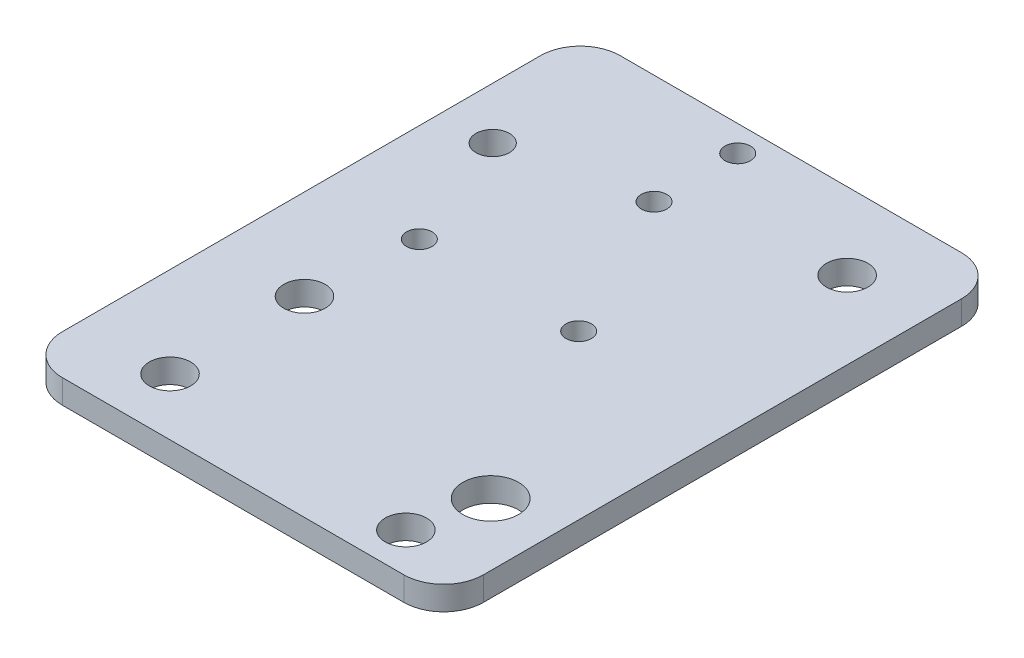
SolidWorks part; units mm, degrees
material "6061 合金"
ref_plane "前视基准面" through (0, 0, 0) normal (0, 0, 1) x (1, 0, 0)
ref_plane "上视基准面" through (0, 0, 0) normal (0, 1, 0) x (1, 0, 0)
ref_plane "右视基准面" through (0, 0, 0) normal (1, 0, 0) x (0, 0, -1)
sketch "草图1" plane through (0, 0, 0) normal (0, 1, 0) x (1, 0, 0)
  line L0 (-7.5, -1000) -> (-7.5, 49000) construction
  line L1 (-17.5, -35) -> (17.5, -35)
  line L2 (-17.5, -35) -> (-17.5, 35)
  line L3 (-17.5, 35) -> (17.5, 35)
  line L4 (17.5, -35) -> (17.5, 35)
  line L5 (0, 35) -> (0, -35) construction
  line L6 (-17.5, 0) -> (17.5, 0) construction
  circle A0 centre (-7.5, 22.5) radius 2.6
  circle A1 centre (-7.5, 0) radius 2.6
  circle A2 centre (-7.5, -22.5) radius 2.6
  circle A3 centre (-7.5, 10) radius 2.6
  circle A4 centre (-7.5, -10) radius 2.6
  point P0 (0, 0)
  dimension "D1" = 45
  dimension "D2" = 5.2
  dimension "D4" = 22.5
  dimension "D8" = 20
  dimension "D5" = 10
  dimension "D6" = 70
  dimension "D7" = 35
  dimension "D3" = 3
extrude "主板" add sketch "草图1" along normal blind 3
sketch "草图2" plane through (0, 3, 0) normal (0, 1, 0) x (1, 0, 0)
  line L0 (-1000, 0) -> (49000, 0) construction
  circle A0 centre (10, 0) radius 2.1
  dimension "D1" = 4.2
  dimension "D2" = 10
extrude "M4铝柱" cut sketch "草图2" against normal blind 3
sketch "草图3" plane through (0, 3, 0) normal (0, 1, 0) x (1, 0, 0)
  circle A0 centre (-7.5, 0) radius 2.6 construction
  circle A1 centre (-7.5, 0) radius 2.6 construction
  circle A2 centre (-7.5, -10) radius 2.6 construction
  circle A3 centre (-7.5, 10) radius 2.6 construction
  circle A4 centre (-7.5, -10) radius 2.6
  circle A5 centre (-7.5, 10) radius 2.6
extrude "填补" add sketch "草图3" against normal through all
sketch "草图4" plane through (0, 3, 0) normal (0, 1, 0) x (1, 0, 0)
  line L1 (-7.5, -22.5) -> (10, -22.5) construction
  line L2 (-7.5, -22.5) -> (-7.5, 22.5) construction
  line L3 (-7.5, 22.5) -> (10, 22.5) construction
  line L4 (10, -22.5) -> (10, 22.5) construction
  line L5 (1.25, 22.5) -> (1.25, -22.5) construction
  line L6 (-7.5, 0) -> (10, 0) construction
  circle A0 centre (-7.5, 22.5) radius 2.6 construction
  circle A1 centre (10, 0) radius 2.1 construction
  circle A2 centre (10, 22.5) radius 2.1
  circle A3 centre (10, -22.5) radius 2.1
  point P0 (1.25, 0)
extrude "摩擦轮垫板" cut sketch "草图4" against normal through all
sketch "草图5" plane through (0, 3, 0) normal (0, 1, 0) x (1, 0, 0)
  line L0 (17.5, 35) -> (-17.5, 35) construction
  line L1 (17.5, -35) -> (66.5, -35) construction
  line L2 (17.5, -35) -> (17.5, 35) construction
  line L3 (17.5, 35) -> (66.5, 35) construction
  line L4 (66.5, -35) -> (66.5, 35) construction
  line L5 (0, -1000) -> (0, 49000) construction
  line L6 (-17.5, 35) -> (-66.5, 35)
  line L7 (-66.5, -35) -> (-66.5, 35)
  line L8 (-17.5, -35) -> (-66.5, -35)
  line L9 (-17.5, -35) -> (-17.5, 35)
  dimension "D1" = 49
extrude "EXTRA" add sketch "草图5" against normal through all
fillet "圆角5" [suppressed] radius 5
sketch "草图6" plane through (0, 3, 0) normal (0, 1, 0) x (1, 0, 0)
  line L0 (-999.7092, 0) -> (49000.2908, 0) construction
  line L2 (-40.5, -989.9006) -> (-40.5, 49010.0994) construction
  line L3 (-7.5, -977.5) -> (-7.5, 49022.5) construction
  circle A0 centre (-44.5, 0) radius 2.1
  circle A1 centre (-36.5, 0) radius 2.1
  dimension "D1" = 4.2
  dimension "D3" = 8
  dimension "D2" = 33
extrude "垂直板接件" cut sketch "草图6" against normal blind 10
sketch "草图7" plane through (0, 3, 0) normal (0, 1, 0) x (1, 0, 0)
  line L0 (-1000, 0) -> (49000, 0) construction
  line L1 (0, -1000) -> (0, 49000) construction
  circle A0 centre (-60, 17.5) radius 2.1
  circle A1 centre (-60, 17.5) radius 5 construction
  circle A2 centre (-60, -17.5) radius 2.1
  dimension "D1" = 4.2
  dimension "D2" = 10
  dimension "D4" = 60
  dimension "D3" = 35
extrude "ETRA铝柱" cut sketch "草图7" against normal blind 10
sketch "草图8" [suppressed] plane through (0, 3, 0) normal (0, 1, 0) x (1, 0, 0)
  line L0 (-17.5, 30) -> (-17.5, -30) construction
  line L1 (17.5, 30) -> (-17.5, 30)
  line L2 (17.5, 30) -> (17.5, 55)
  line L3 (17.5, 55) -> (-17.5, 55)
  line L4 (-17.5, 30) -> (-17.5, 55)
  line L5 (0, -1000) -> (0, 49000) construction
  line L6 (-1000, 0) -> (49000, 0) construction
  line L7 (17.5, -55) -> (-17.5, -55)
  line L8 (-17.5, -30) -> (-17.5, -55)
  line L9 (17.5, -30) -> (-17.5, -30)
  line L10 (17.5, -30) -> (17.5, -55)
  dimension "D1" = 110
extrude "ETRA2" [suppressed] add sketch "草图8" against normal through all
sketch "草图9" [suppressed] plane through (0, 3, 0) normal (0, 1, 0) x (1, 0, 0)
  line L0 (-1000.6559, 0) -> (48999.3441, 0) construction
  line L1 (0, -1000) -> (0, 49000) construction
  line L2 (-7.5, -977.5) -> (-7.5, 49022.5) construction
  line L3 (10, -1000) -> (10, 49000) construction
  circle A0 centre (-7.5, 0) radius 2.6
  circle A1 centre (-7.5, -22.5) radius 2.6 construction
  circle A2 centre (-7.5, 45) radius 2.6
  circle A3 centre (-7.5, -45) radius 2.6
  circle A4 centre (10, 45) radius 2.1
  circle A5 centre (10, 0) radius 2.1 construction
  circle A6 centre (10, -45) radius 2.1
  dimension "D1" = 2
  dimension "D2" = 90
  dimension "D3" = 90
extrude "ETRA2铝柱" [suppressed] cut sketch "草图9" against normal blind 10
sketch "草图10" plane through (0, 0, 0) normal (0, -1, 0) x (1, 0, 0)
  line L0 (-66.5, 35) -> (17.5, 35) construction
  line L1 (-21.5, 31.75) -> (-43.5, 31.75) construction
  line L2 (-21.5, 31.75) -> (-21.5, 21.25) construction
  line L3 (-21.5, 21.25) -> (-43.5, 21.25) construction
  line L4 (-43.5, 31.75) -> (-43.5, 21.25) construction
  line L5 (-32.5, 21.25) -> (-32.5, 31.75) construction
  line L6 (-21.5, 26.5) -> (-43.5, 26.5) construction
  line L7 (-18.5, 18.5) -> (-46.5, 18.5) construction
  line L8 (-18.5, 18.5) -> (-18.5, 34.5) construction
  line L9 (-18.5, 34.5) -> (-46.5, 34.5) construction
  line L10 (-46.5, 18.5) -> (-46.5, 34.5) construction
  line L11 (-32.5, 34.5) -> (-32.5, 18.5) construction
  line L12 (-18.5, 26.5) -> (-46.5, 26.5) construction
  line L13 (-66.5, 35) -> (17.5, 35) construction
  line L14 (-40.5, -998.1832) -> (-40.5, 49001.8168) construction
  line L16 (-1000, 0) -> (49000, 0) construction
  circle A0 centre (-43.5, -21.25) radius 1.6
  circle A1 centre (-21.5, -21.25) radius 1.6 construction
  circle A2 centre (-21.5, -31.75) radius 1.6
  circle A3 centre (-43.5, -31.75) radius 1.6
  circle A4 centre (-60, 17.5) radius 5 construction
  circle A5 centre (-36.5, 0) radius 2.1 construction
  circle A6 centre (-44.5, 0) radius 2.1 construction
  circle A7 centre (-43.5, 21.25) radius 1.6
  circle A8 centre (-21.5, 31.75) radius 1.6
  circle A9 centre (-43.5, 31.75) radius 1.6
  circle A10 centre (-21.5, 21.25) radius 1.6 construction
  circle A11 centre (-21.5, 21.25) radius 3.5
  circle A12 centre (-21.5, -21.25) radius 3.5
  point P0 (-32.5, 26.5)
  point P4 (-32.5, 26.5)
  dimension "D5" = 10
  dimension "D7" = 3.2
  dimension "D8" = 0.5
  dimension "D9" = 7
  dimension "D1" = 22
  dimension "D2" = 10.5
  dimension "D3" = 28
  dimension "D4" = 16
  dimension "D6" = 8
extrude "限位开关" cut sketch "草图10" against normal through all
fillet "圆角5.0" radius 5 4 edges at (17.5, 1.5, -35) (-66.5, 1.5, -35) (17.5, 1.5, 35) (-66.5, 1.5, 35)
fillet "圆角5.1" [suppressed] radius 5
sketch "草图12" plane through (0, 3, 0) normal (0, 1, 0) x (1, 0, 0)
  circle A0 centre (-36.5, 0) radius 2.1
  circle A1 centre (-44.5, 0) radius 2.1
extrude "凸台-拉伸1" add sketch "草图12" against normal up to surface (3 mm away) up to face at (-21.5, 0, 30.15)
sketch "草图13" plane through (0, 3, 0) normal (0, 1, 0) x (1, 0, 0)
  circle A0 centre (-52.5, 0) radius 1.5
  circle A1 centre (-28.5, 0) radius 1.5
extrude "切除-拉伸1" cut sketch "草图13" against normal through all
sketch "草图15" plane through (0, 3, 0) normal (0, 1, 0) x (1, 0, 0)
  line L0 (-13.6537, 35) -> (-13.6537, -35)
  line L1 (12.5, 35) -> (-61.5, 35) construction
  line L2 (-61.5, -35) -> (12.5, -35) construction
  line L3 (-13.6537, -35) -> (19.0047, -35)
  line L4 (19.0047, -35) -> (19.0047, 35)
  line L5 (19.0047, 35) -> (-13.6537, 35)
extrude "切除-拉伸4" cut sketch "草图15" against normal through all
fillet "圆角6" radius 5 2 edges at (-13.6537, 1.5, -35) (-13.6537, 1.5, 35)
sketch "草图16" plane through (0, 0, 0) normal (0, -1, 0) x (1, 0, 0)
  circle A0 centre (-21.5, 31.75) radius 1.6
  circle A1 centre (-21.5, -31.75) radius 1.6034
extrude "凸台-拉伸2" add sketch "草图16" against normal up to surface (3 mm away) up to face at (-52.5, 3, 1.5)
sketch "草图17" plane through (0, 3, 0) normal (0, 1, 0) x (1, 0, 0)
  circle A0 centre (-23.3937, -30) radius 2.5
  circle A1 centre (-24.7637, 30) radius 2.5
extrude "切除-拉伸5" cut sketch "草图17" against normal through all
sketch "草图18" plane through (0, 0, 0) normal (0, -1, 0) x (1, 0, 0)
  circle A0 centre (-52.5, 0) radius 1.5
  circle A1 centre (-28.5, 0) radius 1.5
  dimension "D1" = 3
  dimension "D2" = 3
extrude "凸台-拉伸3" add sketch "草图18" against normal up to surface (3 mm away) up to face at (-23.3937, 3, 32.5)
sketch "草图19" plane through (0, 0, 0) normal (0, -1, 0) x (1, 0, 0)
  circle A0 centre (-54.1537, -2.4481) radius 1.2
  circle A1 centre (-34.1537, -2.4481) radius 1.2
  dimension "D1" = 2.4
  dimension "D2" = 2.4
extrude "切除-拉伸6" cut sketch "草图19" against normal through all
sketch "草图20" plane through (0, 0, 0) normal (0, -1, 0) x (1, 0, 0)
  line L0 (-42.1537, 31.6857) -> (-45.1537, 31.6857) construction
  circle A0 centre (-60, 17.5) radius 2.1
  circle A1 centre (-43.5, 21.25) radius 1.6
  circle A2 centre (-43.6537, 31.6857) radius 2.5582
extrude "凸台-拉伸4" add sketch "草图20" against normal up to surface (3 mm away) up to face at (-54.1537, 3, -3.6481)
sketch "草图22" plane through (0, 0, 0) normal (0, -1, 0) x (-1, 0, 0)
  circle A0 centre (21.5, 21.25) radius 3.5
  circle A1 centre (24.7637, 30) radius 2.5
extrude "凸台-拉伸5" add sketch "草图22" against normal up to surface (3 mm away) up to face at (-54.1537, 3, -3.6481)
sketch "草图25" plane through (0, 3, 0) normal (0, 1, 0) x (1, 0, 0)
  circle A0 centre (-23.3937, 25.3762) radius 2.5
extrude "切除-拉伸9" cut sketch "草图25" against normal through all
sketch "草图26" plane through (0, 0, 0) normal (0, -1, 0) x (1, 0, 0)
  circle A0 centre (-55.1537, 27.842) radius 2.6
  circle A1 centre (-23.3937, -25.3762) radius 2.6
  circle A2 centre (-23.3937, 30) radius 2.6
  circle A3 centre (-55.1537, 10.9674) radius 2.6
  circle A4 centre (-54.1537, -2.4481) radius 1.6
  circle A5 centre (-34.1537, -2.4481) radius 1.6
  point P10 (-36.458, -2.4481)
  point P11 (-34.1839, -2.4481)
  point P13 (-54.1537, -2.4481)
  point P14 (-49.7923, 2.3873)
  point P17 (-40.8629, 2.0461)
  point P18 (-51.6716, -2.8396)
  point P19 (-54.1537, -2.4481)
  point P20 (-34.3719, -2.4481)
  point P21 (0, 0)
  point P22 (0, 0)
  dimension "D1" = 20
extrude "切除-拉伸10" cut sketch "草图26" against normal through all
